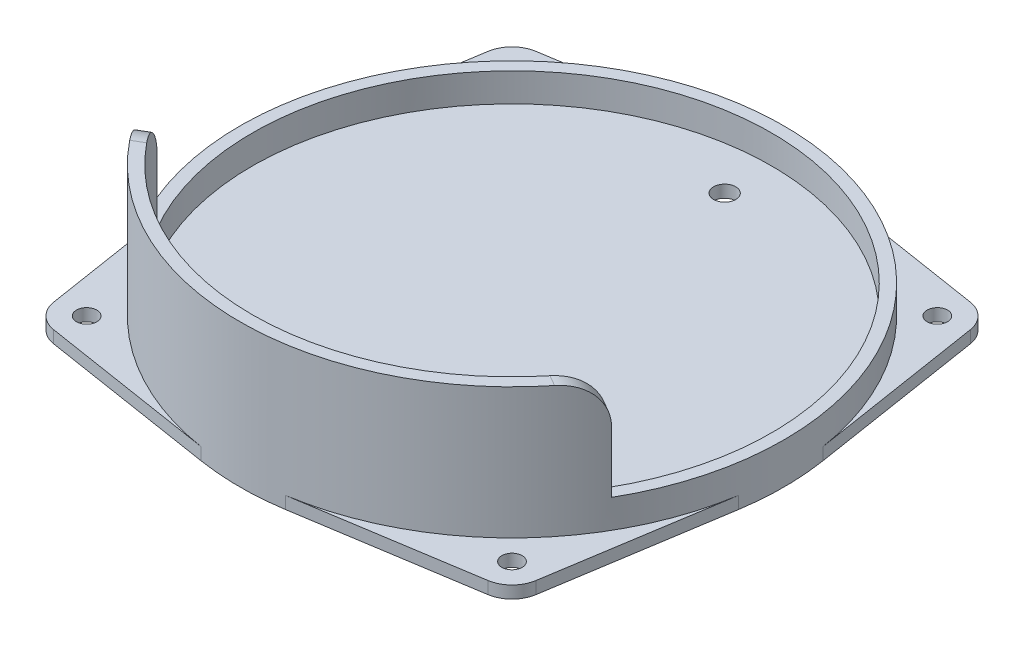
SolidWorks part; units mm, degrees
material "6061-T6 (SS)"
ref_plane "Front Plane" through (0, 0, 0) normal (0, 0, 1) x (1, 0, 0)
ref_plane "Top Plane" through (0, 0, 0) normal (0, 1, 0) x (1, 0, 0)
ref_plane "Right Plane" through (0, 0, 0) normal (1, 0, 0) x (0, 0, -1)
sketch "Sketch1" plane through (0, 0, 0) normal (0, 1, 0) x (1, 0, 0)
  circle A0 centre (0, 0) radius 63.5
  dimension "D1" = 127
extrude "Extrude-Thin1" add sketch "Sketch1" along normal blind 7 thin
sketch "Sketch2" plane through (0, 0, 0) normal (0, 1, 0) x (1, 0, 0)
  line L0 (0, 0) -> (-48.4044, -27.9463) construction
  line L1 (0, 0) -> (0, -52.7423) construction
  line L2 (-54.9926, -31.75) -> (-57.5907, -33.25)
  line L3 (54.9926, -31.75) -> (57.5907, -33.25)
  circle A0 centre (0, 0) radius 63.5 construction
  arc A1 (-54.9926, -31.75) -> (54.9926, -31.75) centre (0, 0) ccw
  circle A2 centre (0, 0) radius 66.5 construction
  arc A3 (-57.5907, -33.25) -> (57.5907, -33.25) centre (0, 0) ccw
  dimension "D1" = 60
extrude "Boss-Extrude1" add sketch "Sketch2" along normal blind 32
sketch "Sketch3" plane through (0, 0, 0) normal (0, 1, 0) x (1, 0, 0)
  line L0 (0, 0) -> (25.2927, 0) construction
  line L1 (0, 0) -> (0, 66.5)
  line L2 (0, 0) -> (52, 52) construction
  line L3 (0, 0) -> (66.5, 0)
  line L5 (10.352, 65.6893) -> (53.0958, 58.9533)
  line L6 (65.6893, 10.352) -> (58.9533, 53.0958)
  circle A0 centre (0, 0) radius 66.5 construction
  arc A2 (58.9533, 53.0958) -> (53.0958, 58.9533) centre (52, 52) ccw
  arc A3 (10.352, 65.6893) -> (0, 66.5) centre (0, 0) ccw
  arc A4 (66.5, 0) -> (65.6893, 10.352) centre (0, 0) ccw
  point P0 (0, 0)
  dimension "D1" = 45
  dimension "D2" = 45
  dimension "D3" = 52
extrude "Boss-Extrude2" add sketch "Sketch3" against normal blind 3
hole_wizard "#10 Clearance Hole1" positions "Sketch5" profile "Sketch4" hole size "#10" standard "ANSI Inch" end condition through all
sketch "Sketch5" plane through (0, 0, 0) normal (0, 1, 0) x (1, 0, 0)
  arc A0 (58.9533, 53.0958) -> (53.0958, 58.9533) centre (52, 52) ccw construction
  point P0 (52, 52)
sketch "Sketch4" plane through (52, 0, -52) normal (1, 0, 0) x (0, 0, 1)
  line L0 (0, 0) -> (0, 3)
  line L1 (0, 3) -> (2.4892, 3)
  line L2 (2.4892, 3) -> (2.4892, 0)
  line L5 (2.4892, 0) -> (0, 0)
  line L11 (0, -6.35) -> (0, 107.95) construction
  dimension "Thru Hole Dia." = 4.9784
  dimension "Thru Hole Depth" = 3
pattern_circular "CirPattern1" count 4 over 360 about axis through (0, 0, 0) along (0, 1, 0) of "Boss-Extrude2", "#10 Clearance Hole1"
fillet "Fillet1" radius 10 2 edges at (56.2917, 32, 32.5) (-56.2917, 32, 32.5)
hole_wizard "1/4-28 Tapped Hole1" positions "Sketch7" profile "Sketch8" tap size "1/4-28" standard "ANSI Inch" end condition through all
sketch "Sketch7" plane through (0, 0, 0) normal (0, 1, 0) x (1, 0, 0)
  point P0 (0, 52)
  dimension "D1" = 52
sketch "Sketch8" plane through (0, 0, -52) normal (1, 0, 0) x (0, 0, 1)
  line L0 (0, 0) -> (0, 3)
  line L1 (0, 3) -> (2.7051, 3)
  line L2 (2.7051, 3) -> (2.7051, 0)
  line L5 (2.7051, 0) -> (0, 0)
  line L11 (0, -6.35) -> (0, 107.95) construction
  dimension "Thru Tap Drill Dia." = 5.4102
  dimension "Thru Tap Drill Depth" = 3
cosmetic thread "Hole Thread1" parameters "D2"=6.35
